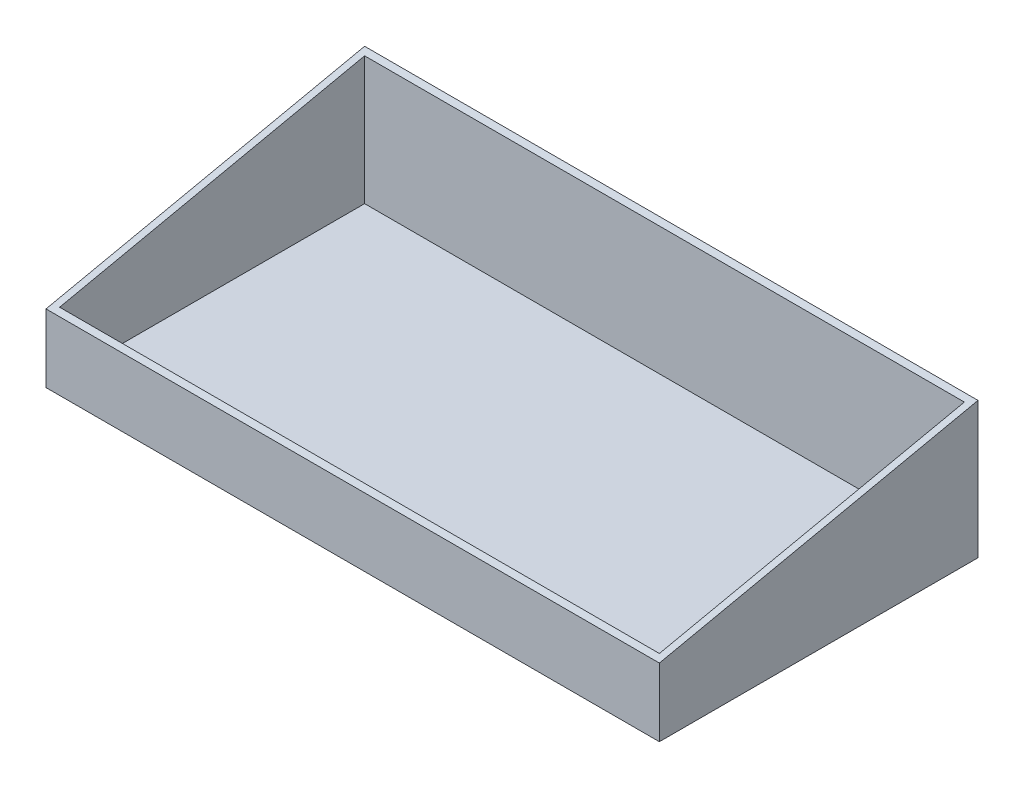
SolidWorks part; units mm, degrees
ref_plane "Alzado" through (0, 0, 0) normal (0, 0, 1) x (1, 0, 0)
ref_plane "Planta" through (0, 0, 0) normal (0, 1, 0) x (1, 0, 0)
ref_plane "Vista lateral" through (0, 0, 0) normal (1, 0, 0) x (0, 0, -1)
sketch "Croquis1" plane through (0, 0, 0) normal (0, 1, 0) x (1, 0, 0)
  line L1 (-180, 93.5) -> (180, 93.5)
  line L2 (-180, 93.5) -> (-180, -93.5)
  line L3 (-180, -93.5) -> (180, -93.5)
  line L4 (180, 93.5) -> (180, -93.5)
  line L5 (-180, 93.5) -> (180, -93.5) construction
  line L6 (-180, -93.5) -> (180, 93.5) construction
  point P0 (0, 0)
  dimension "D1" = 360
  dimension "D2" = 187
extrude "Saliente-Extruir1" add sketch "Croquis1" along normal blind 80
shell "Vaciado1" thickness 4
sketch "Croquis2" plane through (-180, 0, 0) normal (-1, 0, 0) x (0, 0, 1)
  line L0 (-93.5, 80) -> (93.5, 40)
  line L2 (93.5, 80) -> (93.5, 0) construction
  line L3 (93.5, 40) -> (93.5, 80)
  line L4 (93.5, 80) -> (-93.5, 80)
extrude "Cortar-Extruir1" cut sketch "Croquis2" against normal through all
